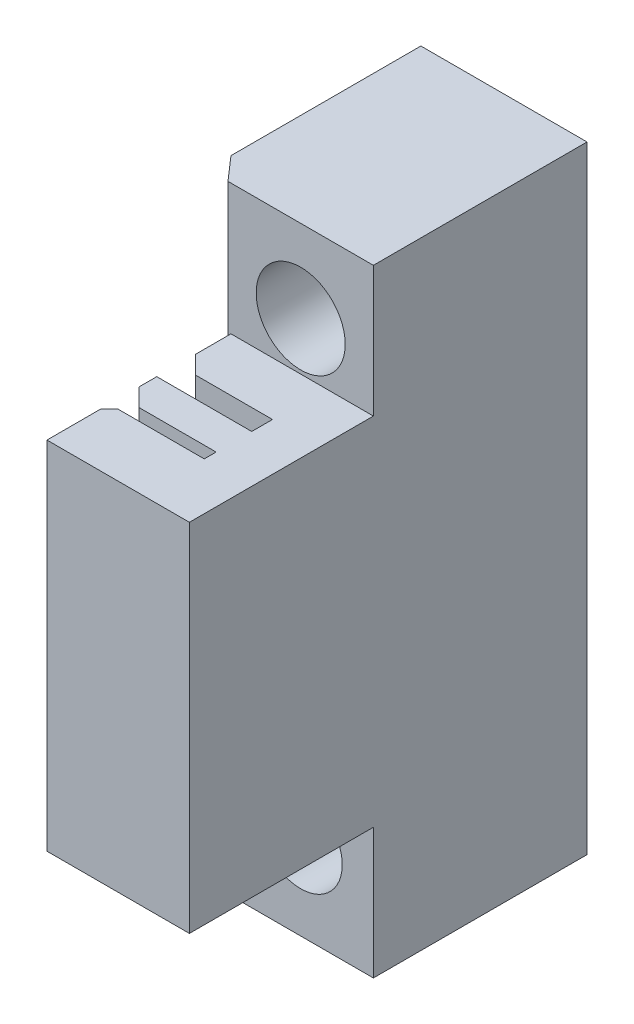
SolidWorks part; units mm, degrees
ref_plane "Front Plane" through (0, 0, 0) normal (0, 0, 1) x (1, 0, 0)
ref_plane "Top Plane" through (0, 0, 0) normal (0, 1, 0) x (1, 0, 0)
ref_plane "Right Plane" through (0, 0, 0) normal (1, 0, 0) x (0, 0, -1)
sketch "Sketch1" plane through (0, 0, 0) normal (0, 1, 0) x (1, 0, 0)
  line L9 (0, 0) -> (14, 0)
  line L10 (14, 0) -> (14, -18)
  line L11 (14, -18) -> (1.75, -18)
  line L12 (1.75, -18) -> (0, -16)
  line L13 (0, -16) -> (0, 0)
  dimension "D1" = 14
  dimension "D2" = 18
  dimension "D3" = 16
  dimension "D4" = 12.25
extrude "Boss-Extrude1" add sketch "Sketch1" along normal mid plane 52
sketch "Sketch2" plane through (0, 0, 0) normal (0, 1, 0) x (1, 0, 0)
  line L0 (14, -18) -> (14, -33.5)
  line L1 (14, -33.5) -> (2, -33.5)
  line L2 (2, -33.5) -> (2, -29.25)
  line L3 (2, -29.25) -> (10, -29.25)
  line L4 (10, -29.25) -> (10, -27.25)
  line L5 (10, -27.25) -> (3.5, -27.25)
  line L6 (3.5, -27.25) -> (2, -25.75)
  line L7 (2, -25.75) -> (2, -24.25)
  line L8 (2, -24.25) -> (10, -24.25)
  line L9 (10, -24.25) -> (10, -22.5)
  line L10 (10, -22.5) -> (3.5, -22.5)
  line L11 (3.5, -22.5) -> (2, -21)
  line L12 (2, -21) -> (2, -18)
  line L13 (2, -18) -> (14, -18)
  dimension "D1" = 15.5
  dimension "D2" = 12
  dimension "D3" = 4.25
  dimension "D4" = 3
  dimension "D5" = 4.5
  dimension "D6" = 2
  dimension "D7" = 135
  dimension "D8" = 1.5
  dimension "D9" = 1.5
  dimension "D10" = 8
extrude "Boss-Extrude2" add sketch "Sketch2" along normal mid plane 30
sketch "Sketch3" plane through (10, 0, 0) normal (-1, 0, 0) x (0, 0, 1)
  line L1 (29.25, 15) -> (28.25, 15)
  line L2 (29.25, 15) -> (29.25, 14)
  line L3 (29.25, 14) -> (28.25, 14)
  line L4 (28.25, 15) -> (28.25, 14)
  dimension "D1" = 1
  dimension "D2" = 1
extrude "Boss-Extrude3" add sketch "Sketch3" along normal up to surface (8 mm away) up to face at (2, 0, 31.375)
chamfer "Chamfer1" distance 0.75 angle 45 1 edges at (2, 14.5, 28.25)
pattern_linear "LPattern1" count 15 spacing 2 along (0, -1, 0) of "Chamfer1", "Boss-Extrude3"
sketch "Sketch5" plane through (10, 0, 0) normal (-1, 0, 0) x (0, 0, 1)
  line L1 (24.25, -15) -> (23.25, -15)
  line L2 (24.25, -15) -> (24.25, -14)
  line L3 (24.25, -14) -> (23.25, -14)
  line L4 (23.25, -15) -> (23.25, -14)
  dimension "D1" = 1
  dimension "D2" = 1
extrude "Boss-Extrude4" add sketch "Sketch5" along normal up to surface (8 mm away) up to face at (2, 0, 25)
chamfer "Chamfer2" distance 0.75 angle 45 1 edges at (2, -14.5, 23.25)
pattern_linear "LPattern2" count 15 spacing 2 along (0, 1, 0) of "Chamfer2", "Boss-Extrude4"
sketch "Sketch6" plane through (0, 0, 18) normal (0, 0, 1) x (1, 0, 0)
  line L0 (7.875, 26) -> (7.875, -26) construction
  line L1 (1.75, 26) -> (14, 26) construction
  line L2 (1.75, -26) -> (14, -26) construction
  line L3 (7.875, 0) -> (16.575, 0) construction
  circle A0 centre (7.875, 19.05) radius 2.1
  circle A1 centre (7.875, -19.05) radius 2.1
  dimension "D3" = 4.2
  dimension "D1" = 38.1
  dimension "D2" = 19.05
extrude "Cut-Extrude1" cut sketch "Sketch6" against normal blind 30
sketch "Sketch7" plane through (0, 0, 18) normal (0, 0, 1) x (1, 0, 0)
  circle A0 centre (7.875, 19.05) radius 3.75
  circle A1 centre (7.875, -19.05) radius 3.5
  dimension "D1" = 7.5
  dimension "D2" = 7
extrude "Cut-Extrude2" cut sketch "Sketch7" against normal blind 7
